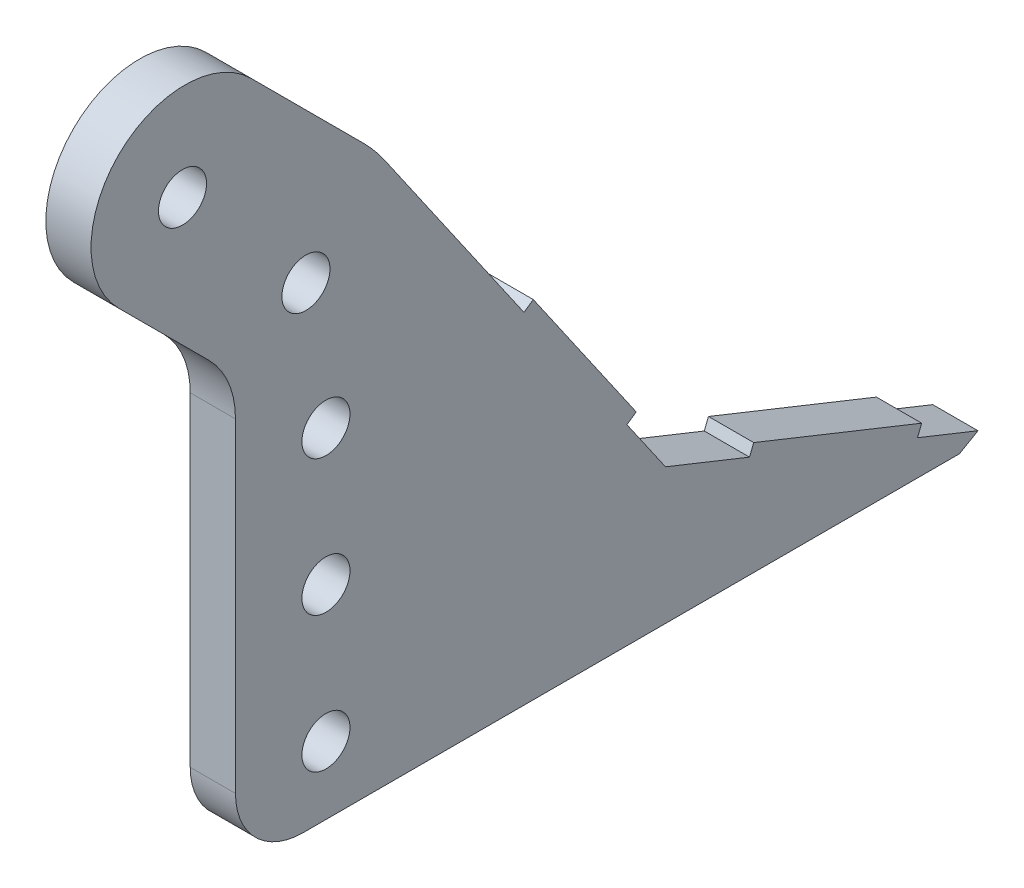
SolidWorks part; units mm, degrees
material "Plain Carbon Steel"
ref_plane "Front Plane" through (0, 0, 0) normal (0, 0, 1) x (1, 0, 0)
ref_plane "Top Plane" through (0, 0, 0) normal (0, 1, 0) x (1, 0, 0)
ref_plane "Right Plane" through (0, 0, 0) normal (1, 0, 0) x (0, 0, -1)
sketch "Sketch1" plane through (0, 0, 0) normal (1, 0, 0) x (0, 0, -1)
  line L0 (305.2991, -24.4357) -> (12.3959, 49.2644)
  line L2 (-10.6887, -49.6628) -> (281.6107, -75.2357)
  line L3 (281.6107, -75.2357) -> (339.725, -133.35)
  line L4 (339.725, -133.35) -> (339.725, -254)
  line L5 (339.725, -254) -> (390.6304, -254)
  line L6 (390.6304, -254) -> (390.6304, -109.767)
  line L7 (390.6304, -109.767) -> (305.2991, -24.4357)
  line L8 (281.6107, -75.2357) -> (305.2991, -24.4357) construction
  line L9 (339.725, -133.35) -> (390.6304, -109.767) construction
  circle A0 centre (0, 0) radius 19.05
  circle A1 centre (0, 0) radius 50.8
  dimension "D1" = 101.6
  dimension "D2" = 38.1
  dimension "D3" = 50.9054
  dimension "D4" = 135
  dimension "D5" = 135
  dimension "D6" = 254
  dimension "D7" = 339.725
  dimension "D8" = 120.65
  dimension "D9" = 50.8
  dimension "D10" = 110
  dimension "D11" = 110
extrude "Boss-Extrude1" add sketch "Sketch1" along normal blind 12.7
fillet "Fillet1" radius 25.4 2 edges at (6.35, -133.35, -339.725) (6.35, -75.2357, -281.6107)
fillet "Fillet2" radius 50.8 2 edges at (6.35, -109.767, -390.6304) (6.35, -24.4357, -305.2991)
hole_wizard "1/2 Clearance Hole1" positions "Sketch3" profile "Sketch2" hole size "1/2" standard "ANSI Inch"
sketch "Sketch3" plane through (12.7, 0, 0) normal (1, 0, 0) x (0, 0, -1)
  line L8 (306.1083, -63.8122) -> (350.246, -107.95)
  line L9 (365.125, -143.871) -> (365.125, -254)
  line L10 (306.1083, -63.8122) -> (350.246, -107.95)
  line L11 (365.125, -143.871) -> (365.125, -254)
  line L12 (339.725, -254) -> (390.6304, -254) construction
  arc A4 (365.125, -143.871) -> (350.246, -107.95) centre (314.325, -143.871) ccw
  arc A5 (365.125, -143.871) -> (350.246, -107.95) centre (314.325, -143.871) ccw
  point P34 (365.125, -234.95)
  point P36 (365.125, -196.85)
  point P38 (365.125, -158.75)
  point P40 (359.5071, -120.65)
  point P42 (324.846, -82.55)
  dimension "D2" = 38.1
  dimension "D3" = 19.05
  dimension "D4" = 38.1
  dimension "D5" = 38.1
  dimension "D6" = 38.1
  dimension "D1" = 25.4
sketch "Sketch2" plane through (12.7, -234.95, -365.125) normal (0, 1, 0) x (0, 0, -1)
  line L0 (0, 0) -> (0, 42.1535)
  line L1 (0, 42.1535) -> (6.7462, 38.1)
  line L2 (6.7462, 38.1) -> (6.7462, 0)
  line L5 (6.7462, 0) -> (0, 0)
  line L10 (0, 42.1535) -> (-6.7462, 38.1) construction
  line L11 (0, -6.35) -> (0, 107.95) construction
  dimension "Hole Dia." = 13.4925
  dimension "Hole Depth" = 38.1
  dimension "Drill Angle" = 118
sketch "Sketch4" plane through (12.7, 0, 0) normal (1, 0, 0) x (0, 0, -1)
  line L0 (288.1478, -81.7728) -> (332.2855, -125.9105) construction
  line L1 (375.7514, -94.888) -> (315.2192, -34.3558) construction
  line L2 (306.8855, -100.5105) -> (324.846, -82.55) construction
  line L3 (324.846, -82.55) -> (325.5076, -81.8884) construction
  line L4 (306.8855, -100.5105) -> (-73.7979, -100.5105)
  line L5 (-73.7979, -100.5105) -> (-73.7979, 83.4217)
  line L6 (-73.7979, 83.4217) -> (344.1297, 83.4217)
  line L7 (344.1297, 83.4217) -> (344.1297, -63.2663)
  line L8 (324.846, -82.55) -> (344.1297, -63.2663) construction
  circle A0 centre (325.5076, -81.8884) radius 26.3356
  circle M6 centre (0, 0) radius 19.05
  line M9 (375.7514, -94.888) -> (315.2192, -34.3558)
  arc M10 (315.2192, -34.3558) -> (291.694, -21.0124) centre (279.2982, -70.2768) ccw
  line M11 (291.694, -21.0124) -> (12.3959, 49.2644)
  arc M12 (12.3959, 49.2644) -> (-10.6887, -49.6628) centre (0, 0) ccw
  line M13 (-10.6887, -49.6628) -> (272.401, -74.4299)
  arc M14 (272.401, -74.4299) -> (288.1478, -81.7728) centre (270.1872, -99.7333) cw
  line M15 (288.1478, -81.7728) -> (332.2855, -125.9105)
extrude "Cut-Extrude1" cut sketch "Sketch4" against normal through all contours A0 M9 M10 M11 M12 M13 M14 M15 M6
sketch "Sketch5" plane through (12.7, 0, 0) normal (1, 0, 0) x (0, 0, -1)
  line L0 (390.6304, -254) -> (555.7304, -254)
  line L1 (555.7304, -254) -> (460.4804, -215.9)
  line L2 (460.4804, -215.9) -> (381.6055, -101.9044)
  line L3 (390.6304, -254) -> (390.6304, -130.809) construction
  line L4 (390.6304, -254) -> (390.6304, -130.809)
  arc A0 (390.6304, -130.809) -> (375.7514, -94.888) centre (339.8304, -130.809) ccw construction
  arc A1 (390.6304, -130.809) -> (381.6055, -101.9044) centre (339.8304, -130.809) ccw
  dimension "D1" = 165.1
  dimension "D2" = 38.1
  dimension "D3" = 69.85
extrude "Boss-Extrude2" add sketch "Sketch5" against normal up to surface (12.7 mm away) up to face at (0, -82.55, -331.5923)
sketch "Sketch6" plane through (12.7, 0, 0) normal (1, 0, 0) x (0, 0, -1)
  line L0 (449.6412, -200.2343) -> (452.2521, -198.4278)
  line L1 (460.4804, -215.9) -> (381.6055, -101.9044) construction
  line L2 (452.2521, -198.4278) -> (423.3474, -156.6527)
  line L3 (423.3474, -156.6527) -> (420.7365, -158.4592)
  line L4 (420.7365, -158.4592) -> (449.6412, -200.2343)
  line L5 (484.0637, -225.3333) -> (485.2429, -222.3854)
  line L6 (555.7304, -254) -> (460.4804, -215.9) construction
  line L7 (485.2429, -222.3854) -> (532.4095, -241.2521)
  line L8 (532.4095, -241.2521) -> (531.2303, -244.2)
  line L9 (531.2303, -244.2) -> (484.0637, -225.3333)
  dimension "D1" = 19.05
  dimension "D2" = 25.4
  dimension "D3" = 50.8
  dimension "D4" = 3.175
extrude "Boss-Extrude3" add sketch "Sketch6" against normal up to surface (12.7 mm away) up to face at (0, -82.55, -331.5923)
fillet "Fillet3" radius 19.05 1 edges at (6.35, -254, -339.725)
chamfer "Chamfer1" distance 12.7 angle 30 1 edges at (6.35, -254, -555.7304)
